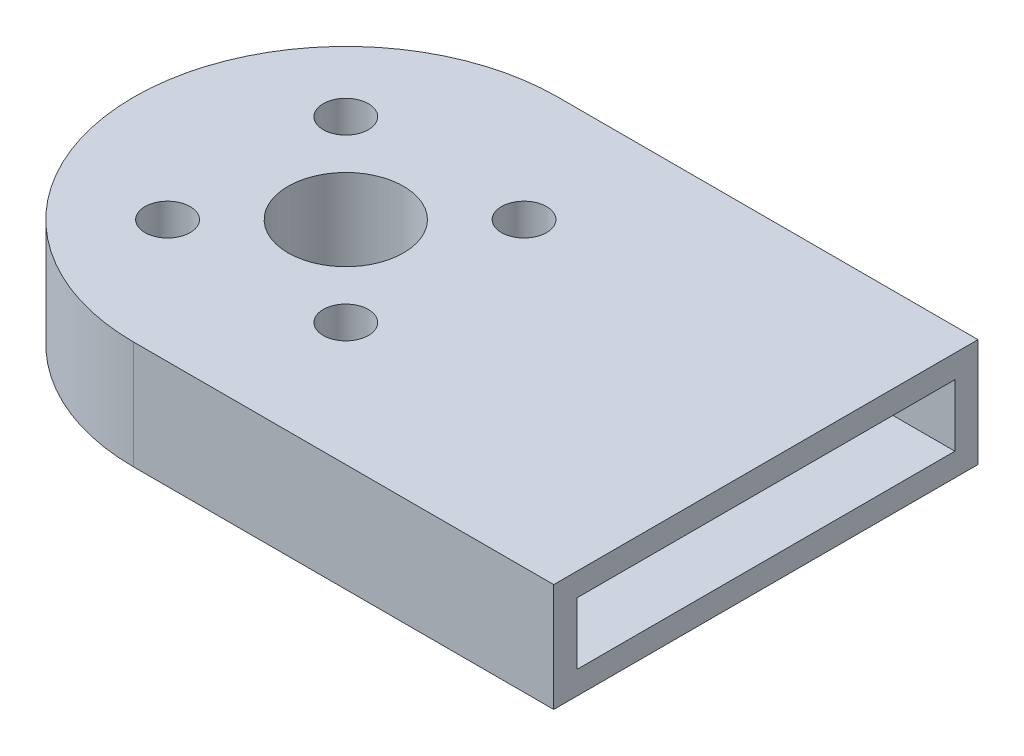
SolidWorks part; units mm, degrees
ref_plane "Front Plane" through (0, 0, 0) normal (0, 0, 1) x (1, 0, 0)
ref_plane "Top Plane" through (0, 0, 0) normal (0, 1, 0) x (1, 0, 0)
ref_plane "Right Plane" through (0, 0, 0) normal (1, 0, 0) x (0, 0, -1)
sketch "Sketch2" plane through (0, 0, 0) normal (0, 1, 0) x (1, 0, 0)
  line L0 (-4.2426, 4.2426) -> (4.2426, -4.2426) construction
  line L1 (4.2426, 4.2426) -> (-4.2426, -4.2426) construction
  line L2 (0, 7.5828) -> (0, -11.9719) construction
  line L3 (0, 10.1) -> (20, 10.1)
  line L4 (20, 10.1) -> (20, -10.1)
  line L5 (20, -10.1) -> (0, -10.1)
  arc A0 (0, 10.1) -> (0, -10.1) centre (0, 0) ccw
  circle A1 centre (-4.2426, 4.2426) radius 1.075
  circle A2 centre (4.2426, 4.2426) radius 1.075
  circle A3 centre (-4.2426, -4.2426) radius 1.075
  circle A4 centre (4.2426, -4.2426) radius 1.075
  circle A5 centre (0, 0) radius 2.75
  point P11 (0, 0)
  point P12 (0, 0)
  dimension "D1" = 20.2
  dimension "D2" = 2.15
  dimension "D3" = 2.15
  dimension "D4" = 2.15
  dimension "D5" = 2.15
  dimension "D6" = 2.15
  dimension "D11" = 5.5
  dimension "D7" = 12
  dimension "D8" = 12
  dimension "D9" = 45
  dimension "D10" = 45
  dimension "D12" = 20
extrude "Boss-Extrude1" add sketch "Sketch2" along normal blind 5.15
sketch "Sketch3" plane through (0, 5.15, 0) normal (0, 1, 0) x (1, 0, 0)
  line L0 (0, 10.1) -> (16.3154, 10.1)
  line L1 (0, -10.1) -> (16.3154, -10.1)
  line L2 (16.3154, 10.1) -> (16.3154, -10.1)
  line L6 (0, -10.1) -> (20, -10.1)
  line L7 (0, -10.1) -> (20, -10.1)
  line L8 (20, -10.1) -> (20, 10.1)
  line L9 (20, -10.1) -> (20, 10.1)
  line L10 (20, 10.1) -> (0, 10.1)
  line L11 (20, 10.1) -> (0, 10.1)
  circle A0 centre (0, 0) radius 10.1 construction
  arc A2 (0, 10.1) -> (0, -10.1) centre (0, 0) ccw
  arc A3 (0, 10.1) -> (0, -10.1) centre (0, 0) ccw
  dimension "D1" = 0
shell "Shell1" thickness 1.1
